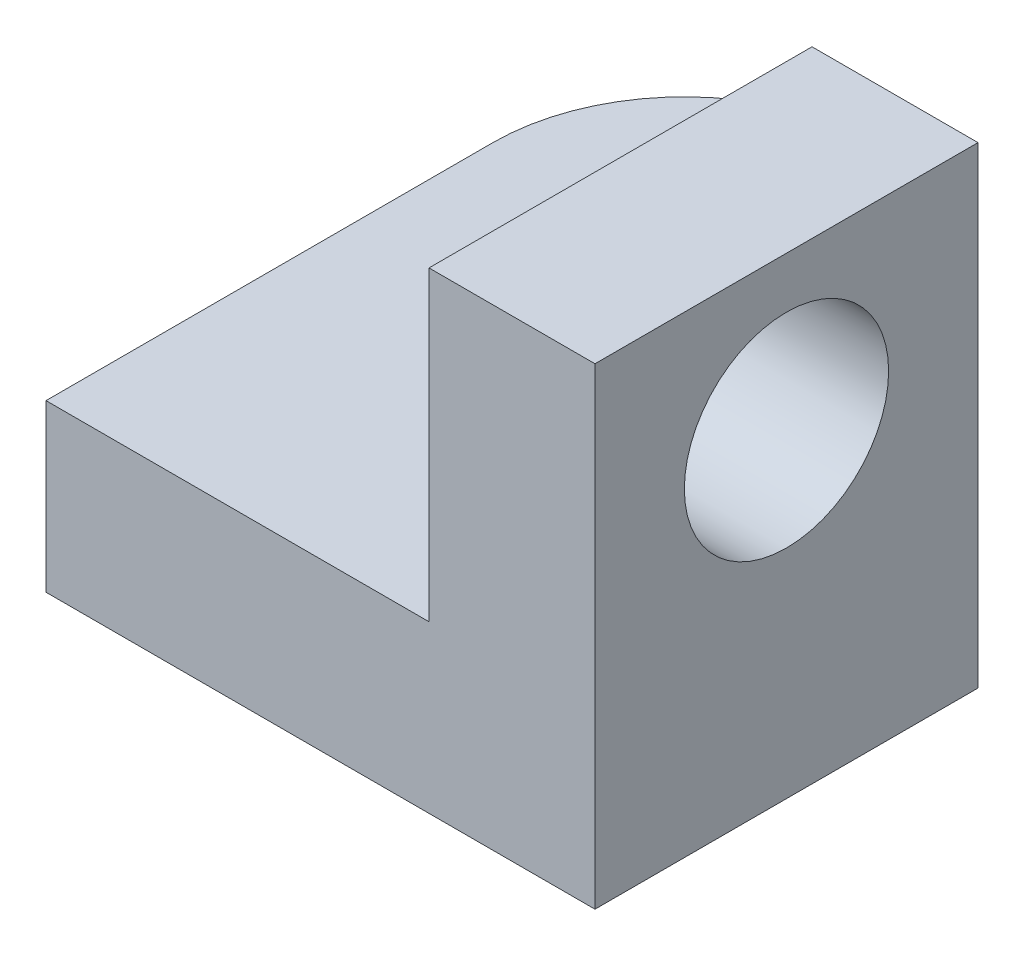
SolidWorks part; units mm, degrees
ref_plane "Front Plane" through (0, 0, 0) normal (0, 0, 1) x (1, 0, 0)
ref_plane "Top Plane" through (0, 0, 0) normal (0, 1, 0) x (1, 0, 0)
ref_plane "Right Plane" through (0, 0, 0) normal (1, 0, 0) x (0, 0, -1)
sketch "Sketch1" plane through (0, 0, 0) normal (0, 1, 0) x (1, 0, 0)
  line L0 (-10.098, -5.6373) -> (19.902, -5.6373)
  line L1 (19.902, -5.6373) -> (19.902, 29.3627)
  line L3 (-10.098, 29.3627) -> (-10.098, -5.6373)
  arc A0 (-10.098, 29.3627) -> (19.902, 29.3627) centre (4.902, 29.3627) cw
  circle A1 centre (4.902, 29.3627) radius 6.5
  dimension "D3" = 13
  dimension "D4" = 15
  dimension "D1" = 30
  dimension "D2" = 35
sketch "Sketch2" plane through (0, 0, 0) normal (1, 0, 0) x (0, 0, -1)
  line L0 (-5.6373, 0) -> (-5.6373, 37)
  line L1 (29.3627, 0) -> (-5.6373, 0) construction
  line L2 (-5.6373, 37) -> (24.3627, 37)
  line L3 (24.3627, 37) -> (24.3627, 0)
  line L4 (-5.6373, 0) -> (24.3627, 0)
  circle A0 centre (9.3627, 25) radius 8
  dimension "D3" = 16
  dimension "D1" = 37
  dimension "D2" = 30
  dimension "D4" = 12
  dimension "D5" = 15
extrude "Boss-Extrude1" add sketch "Sketch1" along normal blind 13 contours A1
extrude "Boss-Extrude2" add sketch "Sketch2" along normal blind 13 from offset 19.9
